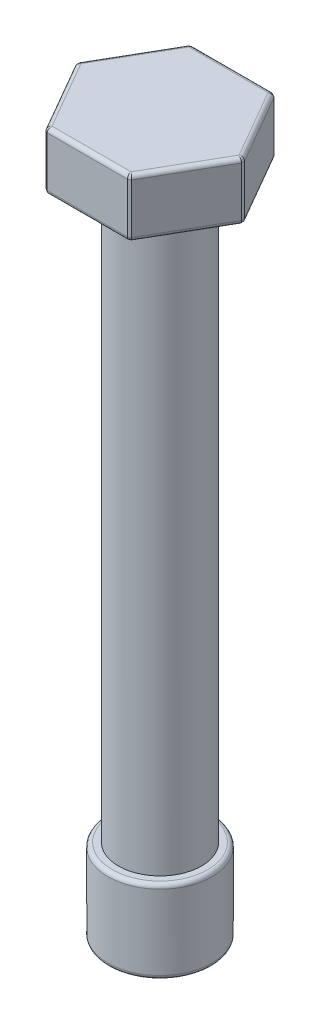
SolidWorks part; units mm, degrees
ref_plane "Front Plane" through (0, 0, 0) normal (0, 0, 1) x (1, 0, 0)
ref_plane "Top Plane" through (0, 0, 0) normal (0, 1, 0) x (1, 0, 0)
ref_plane "Right Plane" through (0, 0, 0) normal (1, 0, 0) x (0, 0, -1)
sketch "Sketch1" plane through (0, 0, 0) normal (0, 0, 1) x (1, 0, 0)
  line L0 (0, 37.6716) -> (0, 0) construction
  line L1 (0, 34.58) -> (-4, 34.58)
  line L2 (-2, 31.78) -> (-2, 4)
  line L3 (-2, 4) -> (-2.5, 4)
  line L4 (-2.5, 4) -> (-2.5, 0)
  line L5 (-2.5, 0) -> (0, 0)
  line L6 (-4, 34.58) -> (-4, 31.78)
  line L7 (-4, 31.78) -> (-2, 31.78)
  line L8 (0, 0) -> (0, 34.58)
  dimension "D1" = 4
  dimension "D2" = 4
  dimension "D3" = 5
  dimension "D4" = 8
  dimension "D5" = 2.8
  dimension "D6" = 27.78
revolve "Revolve1" add sketch "Sketch1" angle 360 about L0
sketch "Sketch2" plane through (0, 34.58, 0) normal (0, 1, 0) x (1, 0, 0)
  line L1 (-4.0415, 0) -> (-2.0207, -3.5)
  line L2 (-2.0207, -3.5) -> (2.0207, -3.5)
  line L3 (2.0207, -3.5) -> (4.0415, 0)
  line L4 (4.0415, 0) -> (2.0207, 3.5)
  line L5 (2.0207, 3.5) -> (-2.0207, 3.5)
  line L6 (-2.0207, 3.5) -> (-4.0415, 0)
  circle A0 centre (0, 0) radius 3.5 construction
  circle A1 centre (0, 0) radius 4.7775
  dimension "D1" = 7
extrude "Cut-Extrude2" cut sketch "Sketch2" against normal up to next and the other way through all
sketch "Sketch3" plane through (0, 0, 0) normal (0, -1, 0) x (1, 0, 0)
  line L1 (0, 1.7321) -> (-1.5, 0.866)
  line L2 (-1.5, 0.866) -> (-1.5, -0.866)
  line L3 (-1.5, -0.866) -> (0, -1.7321)
  line L4 (0, -1.7321) -> (1.5, -0.866)
  line L5 (1.5, -0.866) -> (1.5, 0.866)
  line L6 (1.5, 0.866) -> (0, 1.7321)
  circle A0 centre (0, 0) radius 1.5 construction
  dimension "D1" = 3
extrude "Cut-Extrude3" cut sketch "Sketch3" against normal blind 2.7
fillet "Fillet1" radius 0.2 27 edges at (0, 31.78, 2) (2, 31.78, -3.4641) (0, 31.78, -3.5) (-2, 31.78, -3.4641) (-3.0311, 31.78, -1.75) (-4, 31.78, 0) (-3.0311, 31.78, 1.75) (-2, 31.78, 3.4641) (0, 31.78, 3.5) (2, 31.78, 3.4641) (3.0311, 31.78, 1.75) (4, 31.78, 0) (3.0311, 31.78, -1.75) (4, 34.58, 0) (3.0311, 34.58, 1.75) (2, 34.58, 3.4641) (0, 34.58, 3.5) (-2, 34.58, 3.4641) (-3.0311, 34.58, 1.75) (-4, 34.58, 0) (-3.0311, 34.58, -1.75) (-2, 34.58, -3.4641) (0, 34.58, -3.5) (2, 34.58, -3.4641) (3.0311, 34.58, -1.75) (0, 4, 2.5) (0, 0, 2.5)
sketch "Sketch4" plane through (0, 0, 0) normal (0, 0, 1) x (1, 0, 0)
  line L0 (0, 38.3903) -> (0, -4.2646) construction
